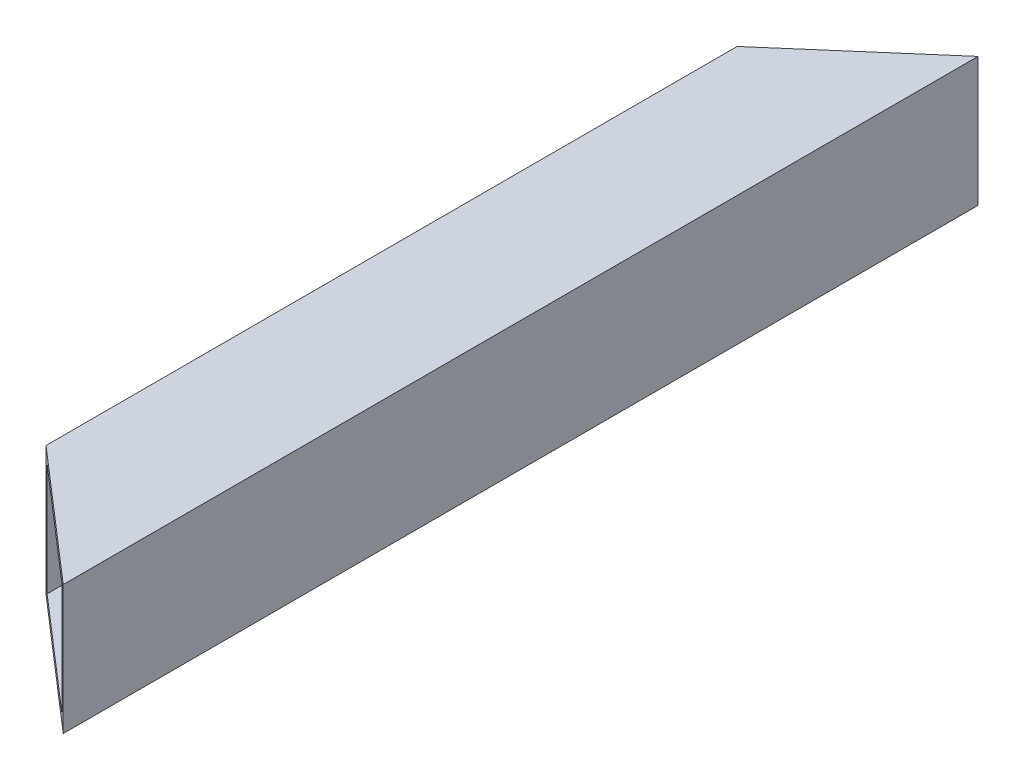
SolidWorks part; units mm, degrees
ref_plane "Front Plane" through (0, 0, 0) normal (0, 0, 1) x (1, 0, 0)
ref_plane "Top Plane" through (0, 0, 0) normal (0, 1, 0) x (1, 0, 0)
ref_plane "Right Plane" through (0, 0, 0) normal (1, 0, 0) x (0, 0, -1)
sketch "Sketch1" plane through (0, 0, 0) normal (0, 0, 1) x (1, 0, 0)
  line L1 (11.049, 11.049) -> (-11.049, 11.049)
  line L2 (11.049, 11.049) -> (11.049, -11.049)
  line L3 (11.049, -11.049) -> (-11.049, -11.049)
  line L4 (-11.049, 11.049) -> (-11.049, -11.049)
  line L5 (11.049, 11.049) -> (-11.049, -11.049) construction
  line L6 (11.049, -11.049) -> (-11.049, 11.049) construction
  line L7 (12.7, 12.7) -> (-12.7, 12.7)
  line L8 (12.7, 12.7) -> (12.7, -12.7)
  line L9 (12.7, -12.7) -> (-12.7, -12.7)
  line L10 (-12.7, 12.7) -> (-12.7, -12.7)
  line L11 (12.7, 12.7) -> (-12.7, -12.7) construction
  line L12 (12.7, -12.7) -> (-12.7, 12.7) construction
  point P0 (0, 0)
  point P6 (0, 0)
  dimension "D3" = 1.651
  dimension "D4" = 1.651
  dimension "D5" = 1.651
  dimension "D2" = 25.4
  dimension "D1" = 25.4
extrude "Boss-Extrude1" add sketch "Sketch1" along normal up to vertex (158.0371 mm away)
sketch "Sketch3" plane through (0, 0, 0) normal (0, 1, 0) x (1, 0, 0)
  line L0 (0, 12.8662) -> (0, -262.1311) construction
  line L1 (0, -13.97) -> (0, 13.97) construction
ref_point "Point1"
sketch "Sketch6" plane through (0, 0, 0) normal (0, 0, -1) x (-1, 0, 0)
  line L4 (12.7, -12.7) -> (12.7, 12.7)
  line L5 (12.7, 12.7) -> (-12.7, 12.7)
  line L6 (-12.7, 12.7) -> (-12.7, -12.7)
  line L7 (-12.7, -12.7) -> (12.7, -12.7)
  line L8 (12.7, -12.7) -> (12.7, 12.7)
  line L9 (12.7, 12.7) -> (-12.7, 12.7)
  line L10 (-12.7, 12.7) -> (-12.7, -12.7)
  line L11 (-12.7, -12.7) -> (12.7, -12.7)
  dimension "D1" = 0
sketch "Sketch7" plane through (0, 0, 0) normal (0, 0, -1) x (-1, 0, 0)
  line L0 (11.049, 11.049) -> (11.049, -11.049) construction
  line L1 (-11.049, 11.049) -> (11.049, 11.049) construction
  line L2 (12.7, 12.7) -> (-12.7, 12.7) construction
  line L3 (12.7, -12.7) -> (12.7, 12.7) construction
  line L4 (-12.7, -12.7) -> (12.7, -12.7) construction
  line L5 (11.049, -11.049) -> (-11.049, -11.049) construction
  line L6 (-11.049, -11.049) -> (-11.049, 11.049) construction
  line L7 (-12.7, 12.7) -> (-12.7, -12.7) construction
  line L8 (11.049, 11.049) -> (11.049, -11.049)
  line L9 (-11.049, 11.049) -> (11.049, 11.049)
  line L10 (12.7, 12.7) -> (-12.7, 12.7)
  line L11 (12.7, -12.7) -> (12.7, 12.7)
  line L12 (-12.7, -12.7) -> (12.7, -12.7)
  line L13 (11.049, -11.049) -> (-11.049, -11.049)
  line L14 (-11.049, -11.049) -> (-11.049, 11.049)
  line L15 (-12.7, 12.7) -> (-12.7, -12.7)
extrude "Boss-Extrude2" add sketch "Sketch7" along normal blind 12.7
ref_plane "Plane1" through (0, 22.7, 0) normal (0, 1, 0) x (1, 0, 0)
sketch "Sketch8" plane through (0, 22.7, 0) normal (0, 1, 0) x (1, 0, 0)
  line L0 (42.1409, 36.5083) -> (-34.6284, -30)
  line L1 (-34.6284, -30) -> (0, -30) construction
  line L2 (0, 12.8662) -> (0, -262.1311) construction
  line L3 (-34.6284, -30) -> (-30, 4.3177) construction
  line L4 (-262.7379, 37.8143) -> (9.4547, -1.3608) construction
  line L5 (-34.6284, -30) -> (-56.5716, 82.7738)
  line L6 (-56.5716, 82.7738) -> (42.1409, 36.5083)
  point P10 (0, 0)
  point P11 (-5.6343, 67.036)
  point P13 (37.2278, 31.9456)
  point P14 (-22.6025, 79.4707)
  point P15 (71.9296, 26.7645)
  point P16 (34.3429, -25.9418)
  point P17 (55.6797, 27.6123)
  point P18 (-53.6683, 7.7242)
  point P19 (-29.7178, 4.2771)
  dimension "D1" = 30
  dimension "D2" = 30
extrude "Cut-Extrude1" cut sketch "Sketch8" against normal through all
sketch "Sketch9" plane through (0, 0, 158.0371) normal (0, 0, 1) x (1, 0, 0)
  line L0 (-12.7, -12.7) -> (-12.7, 12.7) construction
  line L1 (-12.7, 12.7) -> (12.7, 12.7) construction
  line L2 (12.7, -12.7) -> (-12.7, -12.7) construction
  line L3 (12.7, 12.7) -> (12.7, -12.7) construction
  line L4 (-11.049, 11.049) -> (-11.049, -11.049)
  line L5 (11.049, 11.049) -> (-11.049, 11.049)
  line L6 (11.049, -11.049) -> (11.049, 11.049)
  line L7 (-11.049, -11.049) -> (11.049, -11.049)
  line L8 (-11.049, 11.049) -> (-11.049, -11.049)
  line L9 (11.049, 11.049) -> (-11.049, 11.049)
  line L10 (11.049, -11.049) -> (11.049, 11.049)
  line L11 (-11.049, -11.049) -> (11.049, -11.049)
  line L12 (-12.7, -12.7) -> (-12.7, 12.7)
  line L13 (-12.7, 12.7) -> (12.7, 12.7)
  line L14 (12.7, -12.7) -> (-12.7, -12.7)
  line L15 (12.7, 12.7) -> (12.7, -12.7)
  dimension "D1" = 0
extrude "Boss-Extrude3" add sketch "Sketch9" along normal blind 25.4
sketch "Sketch11" plane through (-388.0313, 22.7, 553.3379) normal (0, 1, 0) x (-1, 0, 0)
  line L0 (-358.3373, -391.0271) -> (-356.0474, -423.011) construction
  line L1 (-356.0474, -423.011) -> (-388.0313, -425.3008) construction
  line L3 (-413.9693, -372.8287) -> (-356.0474, -423.011)
  line L4 (-388.0313, -566.2041) -> (-388.0313, -291.2069) construction
  line L5 (-356.0474, -423.011) -> (-328.0545, -334.0452)
  line L6 (-328.0545, -334.0452) -> (-413.9693, -372.8287)
  line L8 (-125.2934, -357.4865) -> (-397.4859, -396.6616) construction
  point P2 (0, 0)
  point P5 (-360.6903, -347.779)
  point P6 (-438.8507, -351.2719)
  point P7 (-328.0545, -334.0452)
  point P14 (-420.098, -367.5189)
  dimension "D1" = 30
  dimension "D2" = 30
extrude "Cut-Extrude2" cut sketch "Sketch11" against normal through all contours L5 L6 L3
equation "\"c1c2Len\"= 250"
equation "\"D1\"= \"c1c2Len\""
equation "\"1inchSquareTubeLen\"=25.4"
equation "\"D2@Sketch1\"=\"1inchSquareTubeLen\""
equation "\"D1@Sketch1\"=\"1inchSquareTubeLen\""
equation "\"squareTubeWallThickness\"=1.651"
equation "\"D5@Sketch1\"=\"squareTubeWallThickness\""
equation "\"D4@Sketch1\"=\"squareTubeWallThickness\""
equation "\"D3@Sketch1\"=\"squareTubeWallThickness\""
